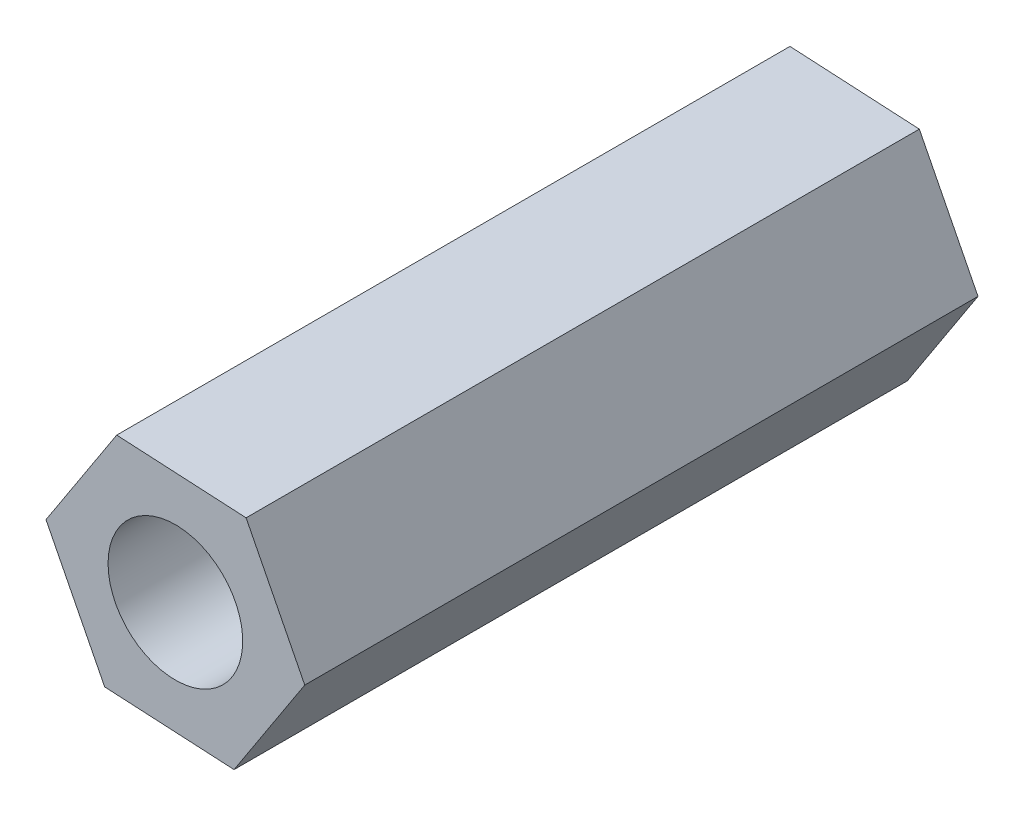
SolidWorks part; units mm, degrees
ref_plane "Front Plane" through (0, 0, 0) normal (0, 0, 1) x (1, 0, 0)
ref_plane "Top Plane" through (0, 0, 0) normal (0, 1, 0) x (1, 0, 0)
ref_plane "Right Plane" through (0, 0, 0) normal (1, 0, 0) x (0, 0, -1)
sketch "Sketch1" plane through (0, 0, 0) normal (0, 0, 1) x (1, 0, 0)
  line L1 (1.5755, 2.4189) -> (-1.3071, 2.5739)
  line L2 (-1.3071, 2.5739) -> (-2.8826, 0.1549)
  line L3 (-2.8826, 0.1549) -> (-1.5755, -2.4189)
  line L4 (-1.5755, -2.4189) -> (1.3071, -2.5739)
  line L5 (1.3071, -2.5739) -> (2.8826, -0.1549)
  line L6 (2.8826, -0.1549) -> (1.5755, 2.4189)
  circle A0 centre (0, 0) radius 2.5 construction
  dimension "D1" = 5
extrude "Boss-Extrude1" add sketch "Sketch1" along normal blind 15
sketch "Sketch2" plane through (0, 0, 0) normal (0, 0, -1) x (-1, 0, 0)
  circle A0 centre (0, 0) radius 1.5
  dimension "D1" = 3
extrude "Cut-Extrude1" cut sketch "Sketch2" against normal through all
